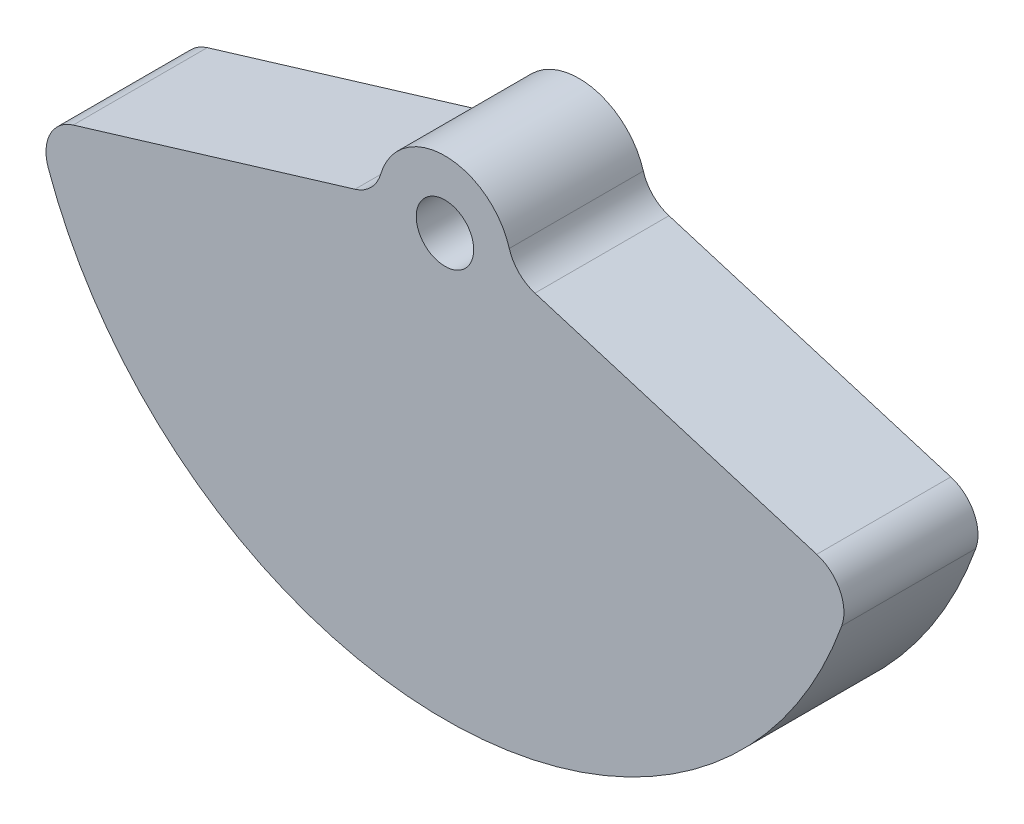
SolidWorks part; units mm, degrees
material "AISI 1020"
ref_plane "Front Plane" through (0, 0, 0) normal (0, 0, 1) x (1, 0, 0)
ref_plane "Top Plane" through (0, 0, 0) normal (0, 1, 0) x (1, 0, 0)
ref_plane "Right Plane" through (0, 0, 0) normal (1, 0, 0) x (0, 0, -1)
sketch "Sketch2" plane through (0, 0, 0) normal (0, 0, 1) x (1, 0, 0)
  line L0 (-246.5413, -61.1756) -> (-59.6528, -4.6021)
  line L1 (-44.45, 0) -> (44.45, 0) construction
  line L2 (59.6528, -4.6021) -> (246.5413, -61.1756)
  line L3 (0, 0) -> (-117.3327, -48.6008) construction
  line L4 (0, 0) -> (0, -279.4) construction
  line L5 (117.3327, -48.6008) -> (0, 0) construction
  arc A0 (-263.1004, -94.0348) -> (263.1004, -94.0348) centre (0, 0) ccw
  circle A1 centre (0, 0) radius 127 construction
  circle A2 centre (0, 0) radius 19.05
  arc A3 (42.644, 12.5418) -> (-42.644, 12.5418) centre (0, 0) ccw
  circle A4 centre (-117.3327, -48.6008) radius 12.7 construction
  circle A5 centre (117.3327, -48.6008) radius 12.7 construction
  arc A6 (59.6528, -4.6021) -> (42.644, 12.5418) centre (67.0119, 19.7085) cw
  arc A7 (-59.6528, -4.6021) -> (-42.644, 12.5418) centre (-67.0119, 19.7085) ccw
  arc A8 (-246.5413, -61.1756) -> (-263.1004, -94.0348) centre (-239.1822, -85.4862) ccw
  arc A9 (246.5413, -61.1756) -> (263.1004, -94.0348) centre (239.1822, -85.4862) cw
  dimension "D1" = 558.8
  dimension "D2" = 254
  dimension "D3" = 38.1
  dimension "D4" = 25.4
  dimension "D7" = 25.4
  dimension "D10" = 25.4
  dimension "D8" = 25.4
  dimension "D5" = 135
  dimension "D6" = 67.5
  dimension "D9" = 25.4
extrude "Boss-Extrude1" add sketch "Sketch2" along normal mid plane 88.9
scale "Scale1" bodies to scale 101 scale about origin uniform scaling yes scale factor 0.083333
